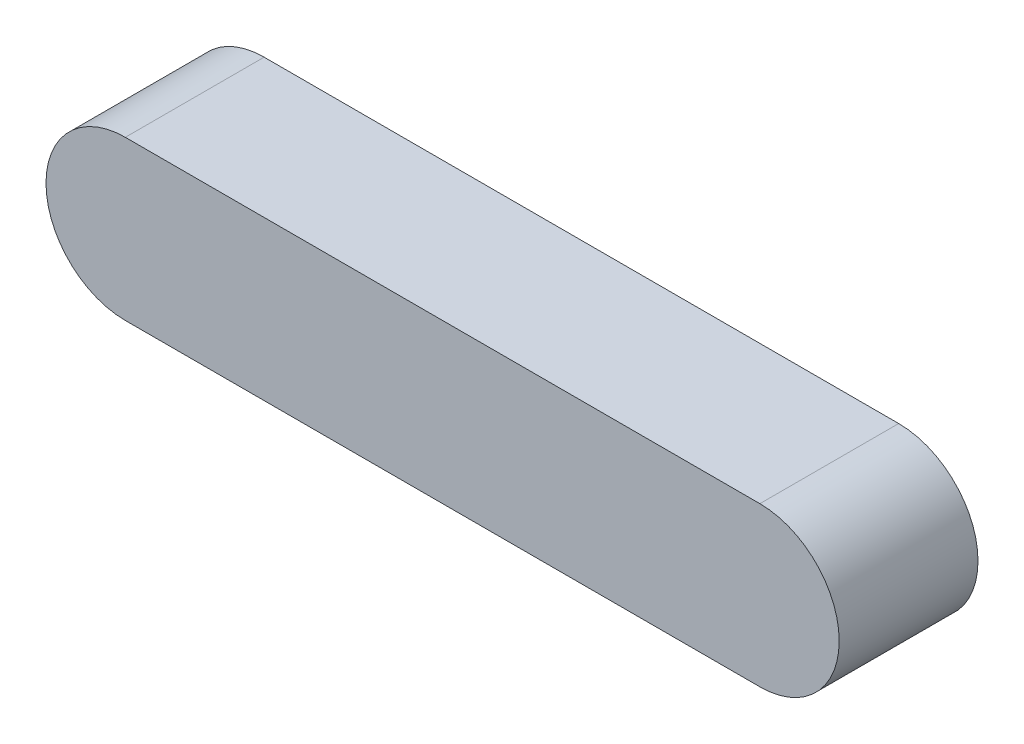
SolidWorks part; units mm, degrees
material "Alloy Steel (SS)"
ref_plane "Front Plane" through (0, 0, 0) normal (0, 0, 1) x (1, 0, 0)
ref_plane "Top Plane" through (0, 0, 0) normal (0, 1, 0) x (1, 0, 0)
ref_plane "Right Plane" through (0, 0, 0) normal (1, 0, 0) x (0, 0, -1)
sketch "Sketch1" plane through (0, 0, 0) normal (0, 0, 1) x (1, 0, 0)
  line L0 (0, 0) -> (32, 0) construction
  line L1 (0, 4) -> (32, 4)
  line L2 (0, -4) -> (32, -4)
  arc A0 (0, 4) -> (0, -4) centre (0, 0) ccw
  arc A1 (32, -4) -> (32, 4) centre (32, 0) ccw
  point P3 (16, 0)
  dimension "D1" = 8
  dimension "D2" = 32
extrude "Boss-Extrude1" add sketch "Sketch1" along normal blind 7
